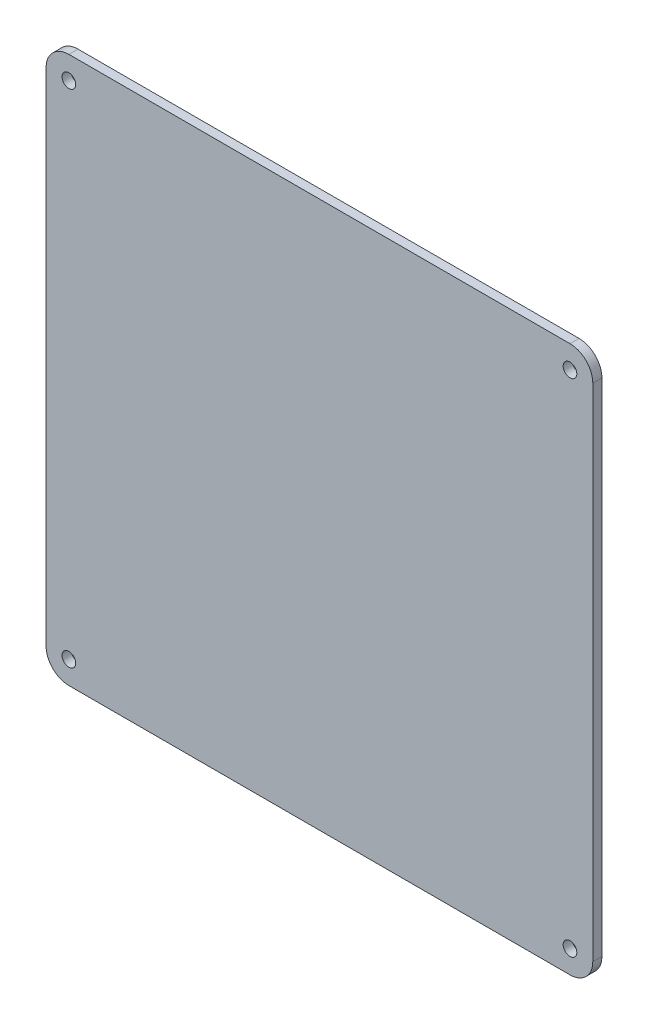
SolidWorks part; units mm, degrees
ref_plane "Plano frontal" through (0, 0, 0) normal (0, 0, 1) x (1, 0, 0)
ref_plane "Plano superior" through (0, 0, 0) normal (0, 1, 0) x (1, 0, 0)
ref_plane "Plano direito" through (0, 0, 0) normal (1, 0, 0) x (0, 0, -1)
sketch "Esboço1" plane through (0, 0, 0) normal (0, 0, 1) x (1, 0, 0)
  line L0 (0, 24.6252) -> (0, 0) construction
  line L1 (-55, 60) -> (55, 60)
  line L2 (-60, 55) -> (-60, -55)
  line L3 (-55, -60) -> (55, -60)
  line L4 (60, 55) -> (60, -55)
  line L5 (-60, 60) -> (60, -60) construction
  line L6 (-60, -60) -> (60, 60) construction
  line L7 (0, 0) -> (20.3911, 0) construction
  circle A0 centre (-55, 55) radius 1.5
  circle A1 centre (55, 55) radius 1.5
  circle A2 centre (-55, -55) radius 1.5
  circle A3 centre (55, -55) radius 1.5
  arc A4 (55, -60) -> (60, -55) centre (55, -55) ccw
  arc A5 (-60, -55) -> (-55, -60) centre (-55, -55) ccw
  arc A6 (-55, 60) -> (-60, 55) centre (-55, 55) ccw
  arc A7 (55, 60) -> (60, 55) centre (55, 55) cw
  point P0 (0, 0)
  point P17 (-46.2409, 46.2409)
  dimension "D4" = 3
  dimension "D1" = 5
  dimension "D2" = 120
  dimension "D3" = 5
  dimension "D5" = 110
extrude "Ressalto-extrusão1" add sketch "Esboço1" along normal blind 2
equation "\"D1@Esboço1\"=\"D3@Esboço1\""
